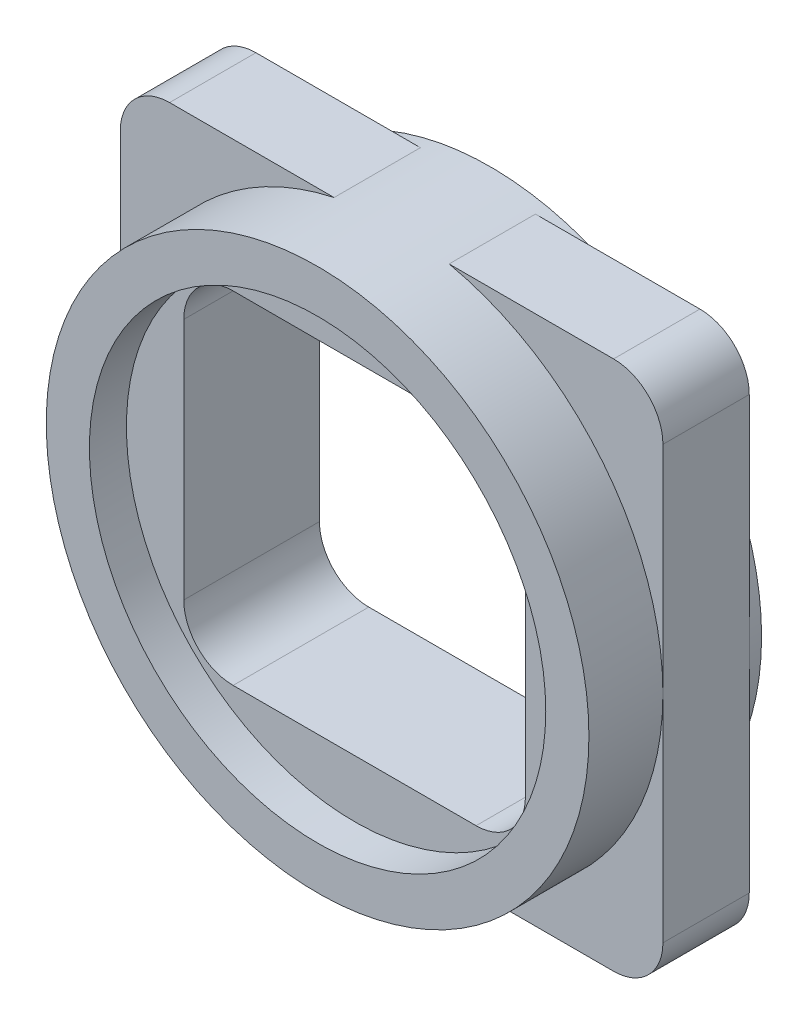
SolidWorks part; units mm, degrees
ref_plane "Front Plane" through (0, 0, 0) normal (0, 0, 1) x (1, 0, 0)
ref_plane "Top Plane" through (0, 0, 0) normal (0, 1, 0) x (1, 0, 0)
ref_plane "Right Plane" through (0, 0, 0) normal (1, 0, 0) x (0, 0, -1)
sketch "Sketch1" plane through (0, 0, 0) normal (0, 0, 1) x (1, 0, 0)
  line L0 (13.85, 0) -> (13.85, -27.7) construction
  line L1 (0, 0) -> (27.7, 0)
  line L2 (0, 0) -> (0, -27.7)
  line L3 (0, -27.7) -> (27.7, -27.7)
  line L4 (27.7, 0) -> (27.7, -27.7)
  line L5 (13.85, -13.85) -> (-20.8882, -13.85) construction
  line L6 (-4.9, 6.6) -> (-4.9, -34.3)
  line L7 (-4.9, 6.6) -> (32.6, 6.6)
  line L8 (32.6, 6.6) -> (32.6, -34.3)
  line L9 (32.6, -34.3) -> (-4.9, -34.3)
  dimension "D1" = 27.7
  dimension "D2" = 27.7
  dimension "D3" = 40.9
  dimension "D4" = 20.45
  dimension "D5" = 37.5
  dimension "D6" = 4.9
extrude "Boss-Extrude1" add sketch "Sketch1" along normal blind 6
sketch "Sketch4" plane through (-4.9, 0, 0) normal (-1, 0, 0) x (0, 0, 1)
  line L0 (0, 3.6) -> (0, -31.3)
  line L1 (6, 3.6) -> (6, -31.3)
  line L2 (6, -34.3) -> (0, -34.3) construction
  line L3 (-4.6231, 10.7134) -> (11.8089, 10.7134)
  line L4 (0, -13.85) -> (6, -13.85) construction
  line L5 (0, 6.6) -> (0, -34.3) construction
  line L6 (6, 6.6) -> (6, -34.3) construction
  line L7 (-4.6231, 10.7134) -> (-4.6231, -36.7194)
  line L8 (-4.6231, -36.7194) -> (11.8089, -36.7194)
  line L9 (11.8089, 10.7134) -> (11.8089, -36.7194)
  arc A0 (6, 3.6) -> (0, 3.6) centre (3, 3.6) ccw
  arc A1 (0, -31.3) -> (6, -31.3) centre (3, -31.3) ccw
  dimension "D1" = 11.8089
  dimension "D2" = 4.6231
  dimension "D3" = 3
  dimension "D5" = 45.0134
  dimension "D6" = 2.4194
extrude "Cut-Extrude1" cut sketch "Sketch4" against normal blind 46
sketch "Sketch5" plane through (0, 0, 6) normal (0, 0, 1) x (1, 0, 0)
  line L0 (-4.9, -13.85) -> (32.6, -13.85) construction
  line L1 (-4.9, 3.6) -> (-4.9, -31.3) construction
  line L2 (32.6, -31.3) -> (32.6, 3.6) construction
  line L4 (-8.15, -35.35) -> (35.85, -35.35)
  line L5 (32.6, 6.6) -> (-4.9, 6.6) construction
  line L6 (13.85, 6.6) -> (13.85, -13.85) construction
  line L7 (-8.15, -35.35) -> (-8.15, 7.65)
  line L8 (-8.15, 7.65) -> (35.85, 7.65)
  line L9 (35.85, -35.35) -> (35.85, 7.65)
  line L10 (-8.15, -35.35) -> (35.85, 7.65) construction
  line L11 (-8.15, 7.65) -> (35.85, -35.35) construction
  dimension "D1" = 43
  dimension "D2" = 44
extrude "Boss-Extrude2" add sketch "Sketch5" along normal blind 1
sketch "Sketch6" plane through (0, 0, 7) normal (0, 0, 1) x (1, 0, 0)
  line L0 (13.85, 7.65) -> (13.85, -35.35) construction
  line L1 (35.85, 7.65) -> (-8.15, 7.65) construction
  line L2 (-8.15, -35.35) -> (35.85, -35.35) construction
  line L3 (-8.15, -13.85) -> (35.85, -13.85) construction
  line L4 (-8.15, 7.65) -> (-8.15, -35.35) construction
  line L5 (35.85, -35.35) -> (35.85, 7.65) construction
  line L7 (4, -27.7) -> (23.7, -27.7)
  line L8 (0, -23.7) -> (0, -4)
  line L9 (4, 0) -> (23.7, 0)
  line L10 (27.7, -23.7) -> (27.7, -4)
  line L11 (0, -27.7) -> (27.7, 0) construction
  line L12 (0, 0) -> (27.7, -27.7) construction
  arc A0 (23.7, -27.7) -> (27.7, -23.7) centre (23.7, -23.7) ccw
  arc A1 (4, -27.7) -> (0, -23.7) centre (4, -23.7) cw
  arc A2 (23.7, 0) -> (27.7, -4) centre (23.7, -4) cw
  arc A3 (0, -4) -> (4, 0) centre (4, -4) cw
  point P12 (13.85, -13.85)
  dimension "D1" = 4
extrude "Cut-Extrude2" cut sketch "Sketch6" against normal blind 1
sketch "Sketch7" plane through (0, 0, 6) normal (0, 0, -1) x (-1, 0, 0)
  line L0 (-35.85, 7.65) -> (8.15, 7.65)
  line L1 (8.15, 7.65) -> (8.15, -35.35)
  line L2 (8.15, -35.35) -> (-35.85, -35.35)
  line L3 (-35.85, -35.35) -> (-35.85, 7.65)
  line L4 (-32.7831, 6.55) -> (5.0831, 6.55)
  line L5 (8.15, 7.65) -> (8.15, -35.35) construction
  line L6 (5.0831, -34.25) -> (-32.7831, -34.25)
  line L7 (8.15, -35.35) -> (-35.85, -35.35) construction
  line L8 (-32.7831, 6.55) -> (-32.7831, -34.25)
  line L9 (-13.85, 6.55) -> (-13.85, -27.7) construction
  line L10 (0, -27.7) -> (-27.7, -27.7) construction
  line L11 (5.0831, 6.55) -> (5.0831, -34.25)
  line L12 (7.05, -34.25) -> (-34.75, -34.25) construction
  line L13 (-34.75, 6.55) -> (7.05, 6.55) construction
  line L14 (-34.75, -34.25) -> (-34.75, 6.55) construction
  line L15 (7.05, 6.55) -> (7.05, -34.25) construction
  dimension "D2" = 3.0669
  dimension "D1" = 1.1
extrude "Boss-Extrude3" add sketch "Sketch7" along normal blind 6
fillet "Fillet1" radius 4 4 edges at (-8.15, 7.65, 3.5) (-8.15, -35.35, 3.5) (35.85, -35.35, 3.5) (35.85, 7.65, 3.5)
sketch "Sketch8" plane through (0, 0, 7) normal (0, 0, 1) x (1, 0, 0)
  line L0 (-8.15, -13.85) -> (35.85, -13.85) construction
  line L1 (-8.15, 3.65) -> (-8.15, -31.35) construction
  line L2 (35.85, -31.35) -> (35.85, 3.65) construction
  line L3 (13.85, 7.65) -> (13.85, -35.35) construction
  line L4 (31.85, 7.65) -> (-4.15, 7.65) construction
  line L5 (-4.15, -35.35) -> (31.85, -35.35) construction
  line L6 (27.7, -23.7) -> (27.7, -4) construction
  line L7 (23.7, 0) -> (4, 0) construction
  line L8 (0, -4) -> (0, -23.7) construction
  line L9 (4, -27.7) -> (23.7, -27.7) construction
  line L10 (27.7, -23.7) -> (27.7, -4)
  line L11 (23.7, 0) -> (4, 0)
  line L12 (0, -4) -> (0, -23.7)
  line L13 (4, -27.7) -> (23.7, -27.7)
  circle A0 centre (13.85, -13.85) radius 22
  arc A1 (27.7, -4) -> (23.7, 0) centre (23.7, -4) ccw construction
  arc A2 (4, 0) -> (0, -4) centre (4, -4) ccw construction
  arc A3 (0, -23.7) -> (4, -27.7) centre (4, -23.7) ccw construction
  arc A4 (23.7, -27.7) -> (27.7, -23.7) centre (23.7, -23.7) ccw construction
  arc A5 (27.7, -4) -> (23.7, 0) centre (23.7, -4) ccw
  arc A6 (4, 0) -> (0, -4) centre (4, -4) ccw
  arc A7 (0, -23.7) -> (4, -27.7) centre (4, -23.7) ccw
  arc A8 (23.7, -27.7) -> (27.7, -23.7) centre (23.7, -23.7) ccw
  dimension "D1" = 44
extrude "Boss-Extrude4" add sketch "Sketch8" along normal blind 3 and the other way blind 8
sketch "Sketch9" plane through (0, 0, 10) normal (0, 0, 1) x (1, 0, 0)
  line L0 (0, -13.85) -> (13.85, -13.85) construction
  line L1 (0, -4) -> (0, -23.7) construction
  line L2 (13.85, -13.85) -> (13.85, 0) construction
  line L3 (23.7, 0) -> (4, 0) construction
  circle A0 centre (13.85, -13.85) radius 22
  circle A1 centre (13.85, -13.85) radius 18.5
  dimension "D1" = 37
  dimension "D2" = 44
extrude "Boss-Extrude5" add sketch "Sketch9" along normal blind 3
